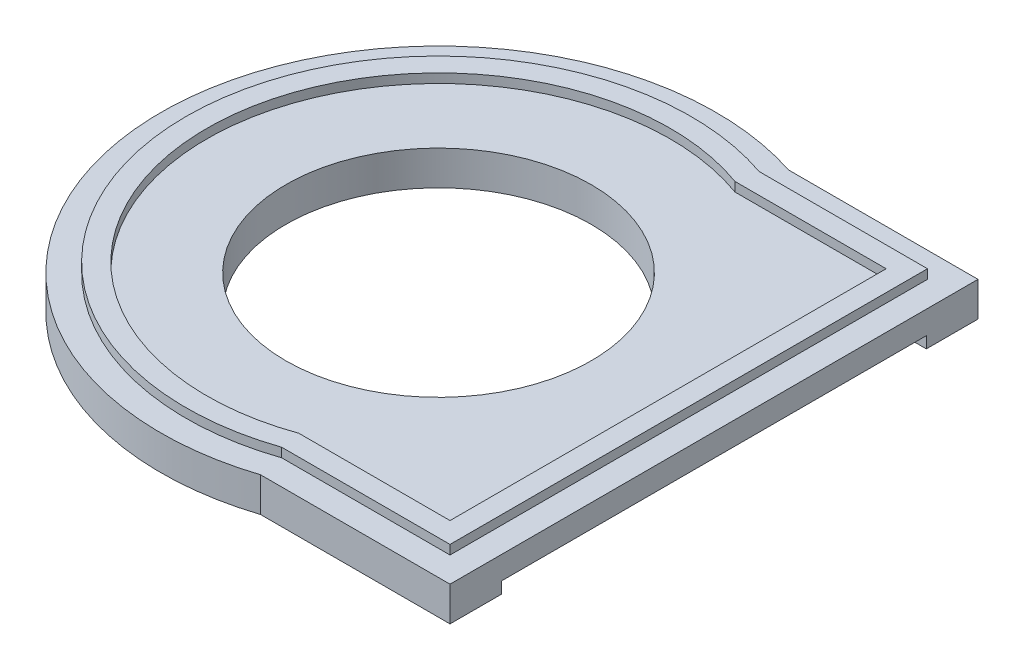
SolidWorks part; units mm, degrees
ref_plane "Спереди" through (0, 0, 0) normal (0, 0, 1) x (1, 0, 0)
ref_plane "Сверху" through (0, 0, 0) normal (0, 1, 0) x (1, 0, 0)
ref_plane "Справа" through (0, 0, 0) normal (1, 0, 0) x (0, 0, -1)
sketch "Эскиз1" plane through (0, 0, 0) normal (0, 1, 0) x (1, 0, 0)
  line L0 (3.7463, -11.5) -> (12, -11.5)
  line L1 (7.8731, 11.5) -> (12, 11.5)
  line L2 (3.7463, 11.5) -> (7.8731, 11.5)
  line L3 (12, -11.5) -> (12, 11.5)
  arc A0 (3.7463, 11.5) -> (3.7463, -11.5) centre (0, 0) ccw
  circle A1 centre (0, 0) radius 6.65
  dimension "D1" = 12.0948
  dimension "D5" = 13.3
  dimension "D2" = 23
  dimension "D3" = 8.2537
  dimension "D4" = 8.2537
extrude "Бобышка-Вытянуть1" add sketch "Эскиз1" along normal blind 1.5
sketch "Эскиз2" plane through (0, 0, 0) normal (0, -1, 0) x (1, 0, 0)
  line L0 (0, 0) -> (12, 0) construction
  line L1 (12, 11.5) -> (12, -11.5) construction
  line L2 (8.65, -9.25) -> (8.65, 9.25)
  line L3 (8.65, 9.25) -> (12, 9.25)
  line L4 (12, 9.25) -> (12, -9.25)
  line L5 (12, -9.25) -> (8.65, -9.25)
  circle A0 centre (0, 0) radius 6.65 construction
  point P5 (8.65, 0)
  point P6 (6.65, 0)
  point P12 (8.65, 0)
  dimension "D1" = 2
  dimension "D2" = 18.5
extrude "Вырез-Вытянуть1" cut sketch "Эскиз2" against normal blind 0.5
sketch "Эскиз3" plane through (0, 1.5, 0) normal (0, 1, 0) x (1, 0, 0)
  line L0 (3.7463, -11.5) -> (12, -11.5) construction
  line L1 (12, -11.5) -> (12, 11.5) construction
  line L2 (12, 11.5) -> (3.7463, 11.5) construction
  line L3 (3.7463, -11.5) -> (12, -11.5)
  line L4 (12, -11.5) -> (12, 11.5)
  line L5 (12, 11.5) -> (3.7463, 11.5)
  arc A0 (3.7463, 11.5) -> (3.7463, -11.5) centre (0, 0) ccw construction
  arc A1 (3.7463, 11.5) -> (3.7463, -11.5) centre (0, 0) ccw
extrude "Вытянуть-Тонкостенный1" add sketch "Эскиз3" along normal blind 0.4 thin thin type one direction reverse wall 2
sketch "Эскиз4" plane through (0, 1.9, 0) normal (0, 1, 0) x (1, 0, 0)
  line L0 (3.7463, -11.5) -> (12, -11.5) construction
  line L1 (12, -11.5) -> (12, 11.5) construction
  line L2 (12, 11.5) -> (3.7463, 11.5) construction
  line L3 (3.7463, -11.5) -> (12, -11.5)
  line L4 (12, -11.5) -> (12, 11.5)
  line L5 (12, 11.5) -> (3.7463, 11.5)
  arc A0 (3.7463, 11.5) -> (3.7463, -11.5) centre (0, 0) ccw construction
  arc A1 (3.7463, 11.5) -> (3.7463, -11.5) centre (0, 0) ccw
extrude "Вырез-Вытянуть-Тонкостенный1" cut sketch "Эскиз4" against normal blind 0.4 thin thin type one direction reverse wall 1.1
